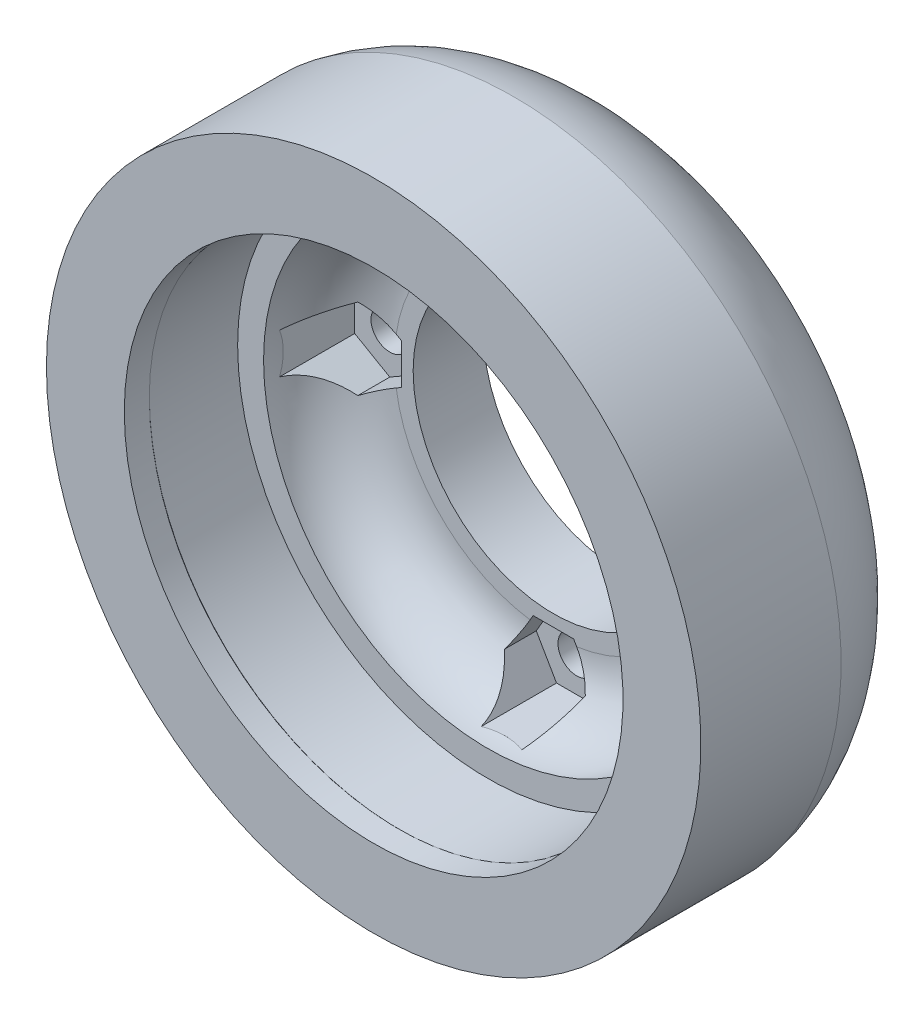
SolidWorks part; units mm, degrees
material "PLA/ABS"
ref_plane "Front Plane" through (0, 0, 0) normal (0, 0, 1) x (1, 0, 0)
ref_plane "Top Plane" through (0, 0, 0) normal (0, 1, 0) x (1, 0, 0)
ref_plane "Right Plane" through (0, 0, 0) normal (1, 0, 0) x (0, 0, -1)
other "Bounding Box"
ref_plane "Default Plane" through (-8.9266, -12.7485, 0) normal (-0.1736, 0.9848, 0) x (0.9848, 0.1736, 0)
sketch "Sketch2" plane through (0, 0, 0) normal (1, 0, 0) x (0, 0, -1)
  line L0 (0, 0) -> (0, 22.5) construction
  line L1 (6, 34) -> (-6, 34)
  line L2 (6, 34) -> (6, 22.5) construction
  line L3 (6, 22.5) -> (-6, 22.5) construction
  line L4 (-6, 34) -> (-6, 22.5) construction
  line L5 (6, 34) -> (-6, 22.5) construction
  line L6 (6, 22.5) -> (-6, 34) construction
  line L9 (-9.525, 44.45) -> (-9.525, 33.873)
  line L13 (24.415, 19.05) -> (24.415, 31.75)
  line L14 (-9.525, 44.45) -> (9.525, 44.45)
  line L15 (-6, 34) -> (-6.127, 33.873)
  line L16 (-6.127, 33.873) -> (-9.525, 33.873)
  line L17 (0, 34) -> (0, 44.45) construction
  line L18 (6, 34) -> (6, 30.48)
  line L19 (24.415, 19.05) -> (14.89, 19.05)
  line L20 (14.89, 19.05) -> (14.89, 21.59)
  line L21 (6, 30.48) -> (24.415, 30.48) construction
  line L22 (0, 0) -> (-9.525, 0) construction
  line L23 (-9.525, 0) -> (-9.525, 33.873) construction
  arc A1 (24.415, 31.75) -> (9.525, 44.45) centre (6.3632, 25.6642) ccw
  arc A2 (6, 30.48) -> (14.89, 21.59) centre (6, 21.59) cw
  point P0 (0, 28.25)
  dimension "D9" = 44.45
  dimension "D10" = 19.05
  dimension "D1" = 22.5
  dimension "D2" = 34
  dimension "D3" = 12
  dimension "D4" = 19.05
  dimension "D5" = 0.127
  dimension "D6" = 45
  dimension "D7" = 18.415
  dimension "D8" = 31.75
  dimension "D11" = 30.48
  dimension "D12" = 9.525
  dimension "D13" = 19.05
revolve "Revolve1" add sketch "Sketch2" angle 360 about L22
sketch "Sketch3" plane through (0, 0, -6) normal (0, 0, 1) x (1, 0, 0)
  line L0 (0, 0) -> (0, 25.4) construction
  line L1 (5.4993, 25.4) -> (2.7496, 30.1625)
  line L2 (2.7496, 30.1625) -> (-2.7496, 30.1625)
  line L3 (-2.7496, 30.1625) -> (-5.4993, 25.4)
  line L4 (-5.4993, 25.4) -> (-2.7496, 20.6375)
  line L5 (-2.7496, 20.6375) -> (2.7496, 20.6375)
  line L6 (2.7496, 20.6375) -> (5.4993, 25.4)
  circle A0 centre (0, 25.4) radius 4.7625 construction
  dimension "D1" = 9.525
  dimension "D2" = 25.4
extrude "Cut-Extrude1" cut sketch "Sketch3" against normal offset from surface (12.065 mm away) 6.35 up to face at (-31.75, 0, -24.415)
sketch "Sketch4" plane through (0, 0, -18.065) normal (0, 0, 1) x (1, 0, 0)
  circle A0 centre (0, 25.4) radius 2.5527
  point P2 (1.1775, 25.3589)
  dimension "D1" = 5.1054
extrude "Cut-Extrude2" cut sketch "Sketch4" against normal through all
pattern_circular "CirPattern1" count 4 over 360 about axis through (0, 0, 0) along (0, 0, 1) of "Cut-Extrude1", "Cut-Extrude2"
